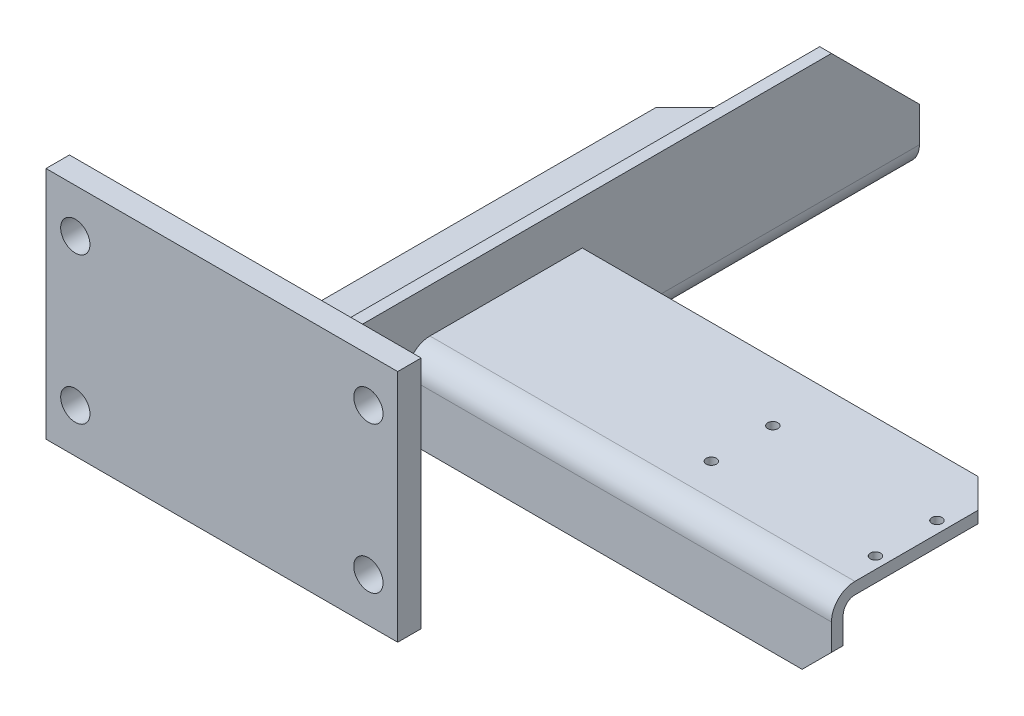
SolidWorks part; units mm, degrees
material "普通碳钢"
ref_plane "Front" through (0, 0, 0) normal (0, 0, 1) x (1, 0, 0)
ref_plane "Top" through (0, 0, 0) normal (0, 1, 0) x (1, 0, 0)
ref_plane "Right" through (0, 0, 0) normal (1, 0, 0) x (0, 0, -1)
sketch "草图1" plane through (0, 0, 0) normal (0, 0, 1) x (1, 0, 0)
  line L13 (0, 0) -> (120, 0)
  line L14 (0, 0) -> (0, 80)
  line L15 (0, 80) -> (120, 80)
  line L16 (120, 0) -> (120, 80)
  dimension "D1" = 80
  dimension "D2" = 120
extrude "凸台-拉伸1" add sketch "草图1" along normal blind 8
sketch "草图2" plane through (0, 0, 8) normal (0, 0, 1) x (1, 0, 0)
  line L4 (0, 40) -> (120, 40) construction
  line L5 (0, 80) -> (0, 0) construction
  line L6 (120, 0) -> (120, 80) construction
  line L7 (0, 15) -> (120, 15) construction
  line L8 (10, 70) -> (10, 10)
  line L9 (10, 10) -> (110, 10)
  line L10 (110, 10) -> (110, 70)
  line L11 (110, 70) -> (10, 70)
  line L12 (10, 70) -> (10, 10) construction
  line L14 (110, 10) -> (110, 70) construction
  line L16 (0, 65) -> (120, 65) construction
  circle A0 centre (10, 65) radius 5
  circle A1 centre (10, 15) radius 5
  circle A2 centre (110, 15) radius 5
  circle A3 centre (110, 65) radius 5
  dimension "D4" = 10
  dimension "D2" = 25
  dimension "D1" = 10
  dimension "D3" = 25
extrude "切除-拉伸1" cut sketch "草图2" against normal up to next
sketch "草图3" plane through (0, 0, 0) normal (0, 0, -1) x (-1, 0, 0)
  line L0 (-30, 20) -> (-82, 20)
  line L4 (-82, 23.9667) -> (-30, 23.9667)
  line L5 (-30, 23.9667) -> (-30, 20)
  line L6 (-86, 27.9667) -> (-86, 70)
  line L7 (-86, 70) -> (-90, 70)
  line L8 (-90, 70) -> (-90, 28)
  line L9 (-120, 0) -> (-120, 80) construction
  line L10 (-120, 80) -> (0, 80) construction
  arc A0 (-90, 28) -> (-82, 20) centre (-82, 28) ccw
  arc A1 (-86, 27.9667) -> (-82, 23.9667) centre (-82, 27.9667) ccw
  point P10 (-88, 70)
  dimension "D3" = 8
  dimension "D4" = 4
  dimension "D1" = 3.9667
  dimension "D2" = 4
  dimension "D5" = 60
  dimension "D6" = 50
  dimension "D7" = 30
  dimension "D8" = 10
extrude "凸台-拉伸2" add sketch "草图3" along normal blind 200
chamfer "倒角1" distance 30 angle 45 2 edges at (88, 70, -200) (30, 21.9834, -200)
sketch "草图5" plane through (0, 20, 0) normal (0, -1, 0) x (1, 0, 0)
  line L0 (60, -70) -> (60, -120) construction
  line L1 (90, -200) -> (90, 0) construction
  line L2 (82, 0) -> (30, 0) construction
  circle A0 centre (60, -70) radius 5
  circle A1 centre (60, -120) radius 5
  dimension "D1" = 30
  dimension "D4" = 10
  dimension "D5" = 10
  dimension "D2" = 70
  dimension "D3" = 50
extrude "切除-拉伸3" cut sketch "草图5" against normal up to next
sketch "草图6" plane through (90, 0, 0) normal (1, 0, 0) x (0, 0, -1)
  line L0 (25, 47) -> (25, 28)
  line L2 (33, 51) -> (85, 51)
  line L3 (85, 51) -> (85, 55)
  line L4 (85, 55) -> (33, 55)
  line L5 (29, 28) -> (29, 47)
  line L7 (0, 70) -> (0, 28) construction
  line L8 (200, 20) -> (0, 20) construction
  line L9 (200, 28) -> (0, 28) construction
  line L10 (25, 28) -> (29, 28)
  arc A2 (33, 51) -> (29, 47) centre (33, 47) ccw
  arc A3 (33, 55) -> (25, 47) centre (33, 47) ccw
  dimension "D6" = 4
  dimension "D7" = 8
  dimension "D1" = 4
  dimension "D2" = 4
  dimension "D3" = 25
  dimension "D4" = 35
  dimension "D5" = 60
extrude "凸台-拉伸3" add sketch "草图6" along normal blind 145
chamfer "倒角2" distance 10 angle 45 2 edges at (235, 28, -27) (235, 53, -85)
sketch "草图7" plane through (0, 55, 0) normal (0, 1, 0) x (1, 0, 0)
  line L0 (155.5813, 44) -> (244.9501, 44) construction
  line L1 (155.5813, 65) -> (244.9501, 65) construction
  line L2 (175, 79.0134) -> (175, 37.5469) construction
  line L3 (231, 79.0134) -> (231, 37.5469) construction
  line L4 (235, 75) -> (235, 33) construction
  line L5 (235, 25) -> (90, 25) construction
  circle A0 centre (231, 65) radius 1.75
  circle A1 centre (231, 44) radius 1.75
  circle A2 centre (175, 44) radius 1.75
  circle A3 centre (175, 65) radius 1.75
  point P10 (200.2657, 44)
  dimension "D5" = 3.5
  dimension "D1" = 21
  dimension "D2" = 56
  dimension "D3" = 4
  dimension "D4" = 19
extrude "切除-拉伸4" cut sketch "草图7" against normal up to next
